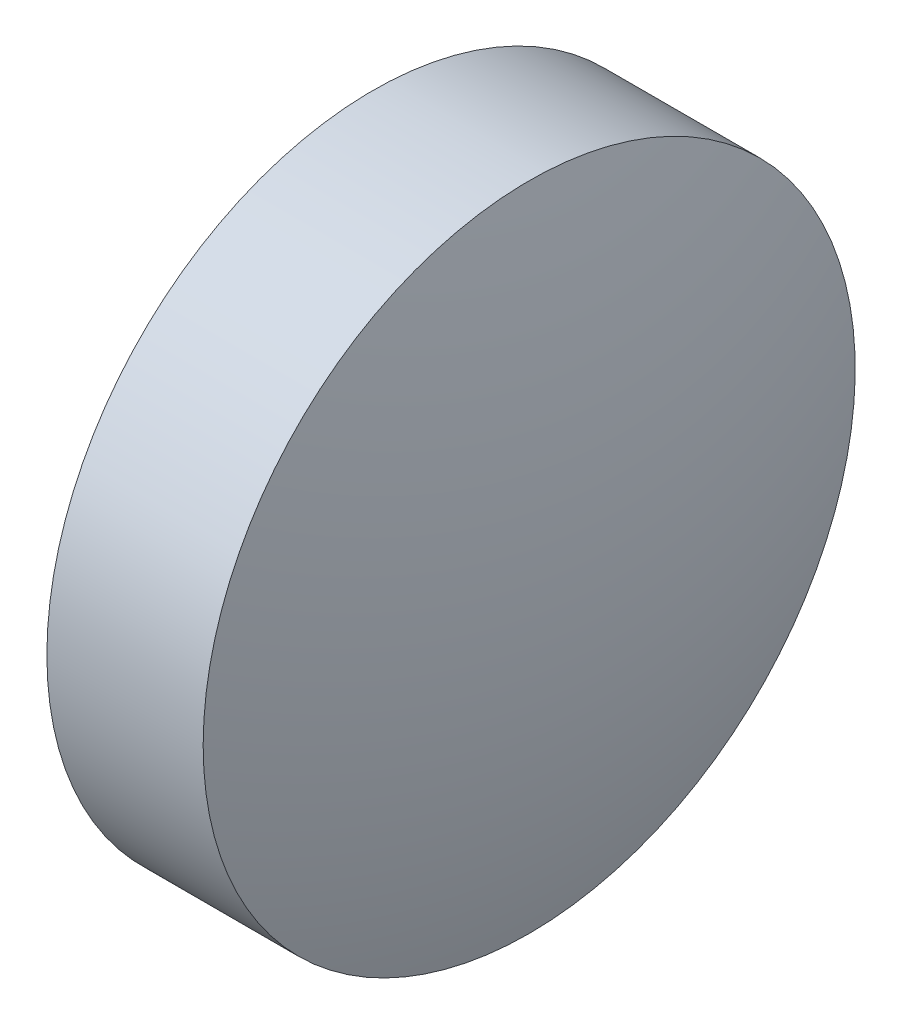
SolidWorks part; units mm, degrees
ref_plane "前视基准面" through (0, 0, 0) normal (0, 0, 1) x (1, 0, 0)
ref_plane "上视基准面" through (0, 0, 0) normal (0, 1, 0) x (1, 0, 0)
ref_plane "右视基准面" through (0, 0, 0) normal (1, 0, 0) x (0, 0, -1)
sketch "草图1" plane through (0, 0, 0) normal (0, 0, 1) x (1, 0, 0)
  line L0 (563.4918, 45.4646) -> (569.6272, 45.4646) construction
  line L1 (564.3535, 45.4646) -> (564.3535, 48.6146)
  line L2 (566.3535, 45.4646) -> (564.3535, 45.4646)
  line L5 (564.3535, 48.6146) -> (565.8635, 48.6146)
  arc A0 (566.3535, 45.4646) -> (565.8635, 48.6146) centre (555.9835, 45.4646) ccw
revolve "旋转1" add sketch "草图1" angle 360 about L0
